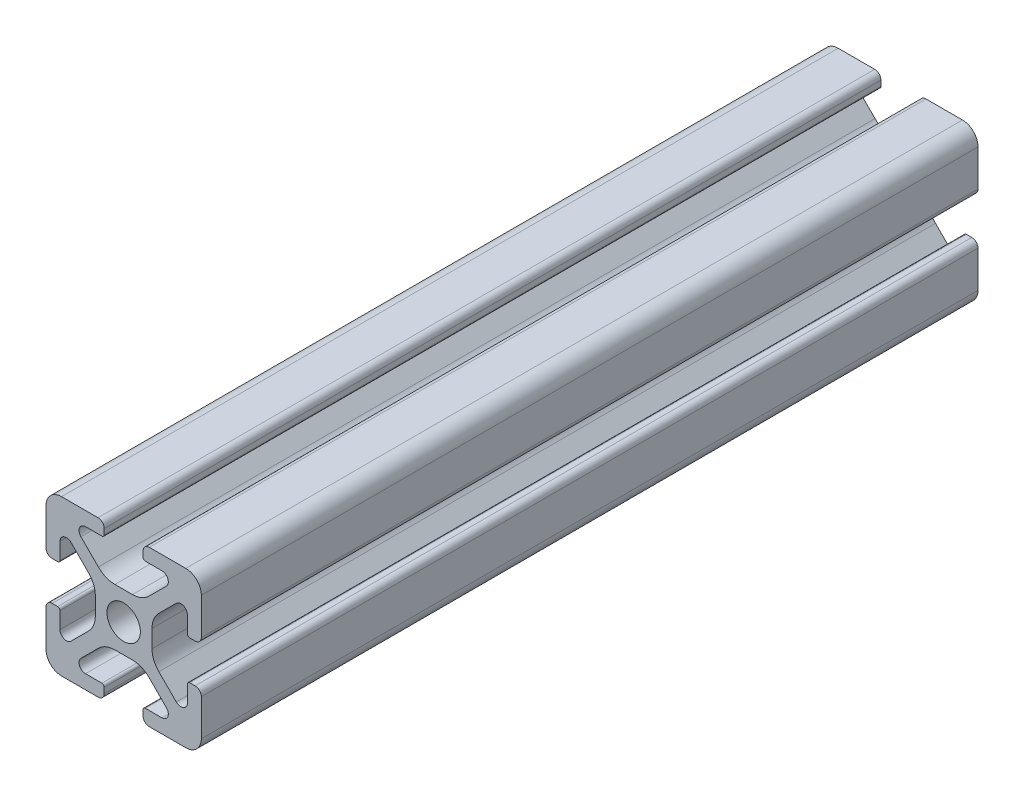
SolidWorks part; units mm, degrees
ref_plane "Front Plane" through (0, 0, 0) normal (0, 0, 1) x (1, 0, 0)
ref_plane "Top Plane" through (0, 0, 0) normal (0, 1, 0) x (1, 0, 0)
ref_plane "Right Plane" through (0, 0, 0) normal (1, 0, 0) x (0, 0, -1)
ref_plane "Plane1" through (0, 0, 0) normal (0, 0, -1) x (-1, 0, 0)
sketch "Sketch1" plane through (0, 0, 0) normal (0, 0, -1) x (-1, 0, 0)
  line L0 (-12.5, 0.8) -> (-12.5, 1.5)
  line L1 (-12.8, 1.8) -> (-14.9176, 1.8)
  line L2 (-15.5062, 3.221) -> (-13.2559, 5.4713)
  line L3 (-11.1346, 6.35) -> (-8.8654, 6.35)
  line L4 (-6.7441, 5.4713) -> (-4.4938, 3.221)
  line L5 (-5.0824, 1.8) -> (-7.2, 1.8)
  line L6 (-7.5, 1.5) -> (-7.5, 0.8)
  line L7 (-6.7, 0) -> (-2, 0)
  line L8 (0, 2) -> (0, 6.7)
  line L9 (-0.8, 7.5) -> (-1.5, 7.5)
  line L10 (-1.8, 7.2) -> (-1.8, 5.0824)
  line L11 (-3.221, 4.4938) -> (-5.4713, 6.7441)
  line L12 (-6.35, 8.8654) -> (-6.35, 11.1346)
  line L13 (-5.4713, 13.2559) -> (-3.221, 15.5062)
  line L14 (-1.8, 14.9176) -> (-1.8, 12.8)
  line L15 (-1.5, 12.5) -> (-0.8, 12.5)
  line L16 (0, 13.3) -> (0, 18)
  line L17 (-2, 20) -> (-6.7, 20)
  line L18 (-7.5, 19.2) -> (-7.5, 18.5)
  line L19 (-7.2, 18.2) -> (-5.0824, 18.2)
  line L20 (-4.4938, 16.779) -> (-6.7441, 14.5287)
  line L21 (-8.8654, 13.65) -> (-11.1346, 13.65)
  line L22 (-13.2559, 14.5287) -> (-15.5062, 16.779)
  line L23 (-14.9176, 18.2) -> (-12.8, 18.2)
  line L24 (-12.5, 18.5) -> (-12.5, 19.2)
  line L25 (-13.3, 20) -> (-18, 20)
  line L26 (-20, 18) -> (-20, 13.3)
  line L27 (-19.2, 12.5) -> (-18.5, 12.5)
  line L28 (-18.2, 12.8) -> (-18.2, 14.9176)
  line L29 (-16.779, 15.5062) -> (-14.5287, 13.2559)
  line L30 (-13.65, 11.1346) -> (-13.65, 8.8654)
  line L31 (-14.5287, 6.7441) -> (-16.779, 4.4938)
  line L32 (-18.2, 5.0824) -> (-18.2, 7.2)
  line L33 (-18.5, 7.5) -> (-19.2, 7.5)
  line L34 (-20, 6.7) -> (-20, 2)
  line L35 (-18, 0) -> (-13.3, 0)
  arc A0 (-12.5, 1.5) -> (-12.8, 1.8) centre (-12.8, 1.5) ccw
  arc A1 (-14.9176, 1.8) -> (-15.5062, 3.221) centre (-14.9176, 2.6324) cw
  arc A2 (-13.2559, 5.4713) -> (-11.1346, 6.35) centre (-11.1346, 3.35) cw
  arc A3 (-8.8654, 6.35) -> (-6.7441, 5.4713) centre (-8.8654, 3.35) cw
  arc A4 (-4.4938, 3.221) -> (-5.0824, 1.8) centre (-5.0824, 2.6324) cw
  arc A5 (-7.2, 1.8) -> (-7.5, 1.5) centre (-7.2, 1.5) ccw
  arc A6 (-7.5, 0.8) -> (-6.7, 0) centre (-6.7, 0.8) ccw
  arc A7 (-2, 0) -> (0, 2) centre (-2, 2) ccw
  arc A8 (0, 6.7) -> (-0.8, 7.5) centre (-0.8, 6.7) ccw
  arc A9 (-1.5, 7.5) -> (-1.8, 7.2) centre (-1.5, 7.2) ccw
  arc A10 (-1.8, 5.0824) -> (-3.221, 4.4938) centre (-2.6324, 5.0824) cw
  arc A11 (-5.4713, 6.7441) -> (-6.35, 8.8654) centre (-3.35, 8.8654) cw
  arc A12 (-6.35, 11.1346) -> (-5.4713, 13.2559) centre (-3.35, 11.1346) cw
  arc A13 (-3.221, 15.5062) -> (-1.8, 14.9176) centre (-2.6324, 14.9176) cw
  arc A14 (-1.8, 12.8) -> (-1.5, 12.5) centre (-1.5, 12.8) ccw
  arc A15 (-0.8, 12.5) -> (0, 13.3) centre (-0.8, 13.3) ccw
  arc A16 (0, 18) -> (-2, 20) centre (-2, 18) ccw
  arc A17 (-6.7, 20) -> (-7.5, 19.2) centre (-6.7, 19.2) ccw
  arc A18 (-7.5, 18.5) -> (-7.2, 18.2) centre (-7.2, 18.5) ccw
  arc A19 (-5.0824, 18.2) -> (-4.4938, 16.779) centre (-5.0824, 17.3676) cw
  arc A20 (-6.7441, 14.5287) -> (-8.8654, 13.65) centre (-8.8654, 16.65) cw
  arc A21 (-11.1346, 13.65) -> (-13.2559, 14.5287) centre (-11.1346, 16.65) cw
  arc A22 (-15.5062, 16.779) -> (-14.9176, 18.2) centre (-14.9176, 17.3676) cw
  arc A23 (-12.8, 18.2) -> (-12.5, 18.5) centre (-12.8, 18.5) ccw
  arc A24 (-12.5, 19.2) -> (-13.3, 20) centre (-13.3, 19.2) ccw
  arc A25 (-18, 20) -> (-20, 18) centre (-18, 18) ccw
  arc A26 (-20, 13.3) -> (-19.2, 12.5) centre (-19.2, 13.3) ccw
  arc A27 (-18.5, 12.5) -> (-18.2, 12.8) centre (-18.5, 12.8) ccw
  arc A28 (-18.2, 14.9176) -> (-16.779, 15.5062) centre (-17.3676, 14.9176) cw
  arc A29 (-14.5287, 13.2559) -> (-13.65, 11.1346) centre (-16.65, 11.1346) cw
  arc A30 (-13.65, 8.8654) -> (-14.5287, 6.7441) centre (-16.65, 8.8654) cw
  arc A31 (-16.779, 4.4938) -> (-18.2, 5.0824) centre (-17.3676, 5.0824) cw
  arc A32 (-18.2, 7.2) -> (-18.5, 7.5) centre (-18.5, 7.2) ccw
  arc A33 (-19.2, 7.5) -> (-20, 6.7) centre (-19.2, 6.7) ccw
  arc A34 (-20, 2) -> (-18, 0) centre (-18, 2) ccw
  arc A35 (-13.3, 0) -> (-12.5, 0.8) centre (-13.3, 0.8) ccw
  circle A36 centre (-10, 10) radius 2.15
extrude "Boss-Extrude1" add sketch "Sketch1" against normal blind 100
equation "\"plate_thickness\" = 3 'thickness of the plate "
equation "\"t_height\" = 150"
equation "\"t_width\" = 240"
equation "\"t_length\" = 282"
equation "\"D1@Boss-Extrude1\"=\"locomotion_height\""
equation "\"connector_D1\" = 70 'the big holes diameter"
equation "\"mtg_hole_D\" = 5.5 'mounting holes"
equation "\"mtg_dfc\" = 40 'mounting hole distance from center"
equation "\"plate_hole_from_edge\" = 9"
equation "\"plate_spacing\" = 1"
equation "\"front_plate_height\" = \"t_height\" + 38"
equation "\"front_plate_width\" = \"t_width\" + 38"
equation "\"side_plate_height\" = \"front_plate_height\""
equation "\"side_plate_length\" = \"t_length\" + 38"
equation "\"top_plate_width\" = \"front_plate_width\""
equation "\"top_plate_length\" = \"side_plate_length\""
equation "\"itx_support_t_slot_length\" = \"t_width\" + (2 * 20.5)"
equation "\"locomotion_length\" = \"t_length\""
equation "\"locomotion_width\" = \"t_width\""
equation "\"locomotion_height\" = 100"
equation "\"itx_mtg_hole_spacing\" = 40"
